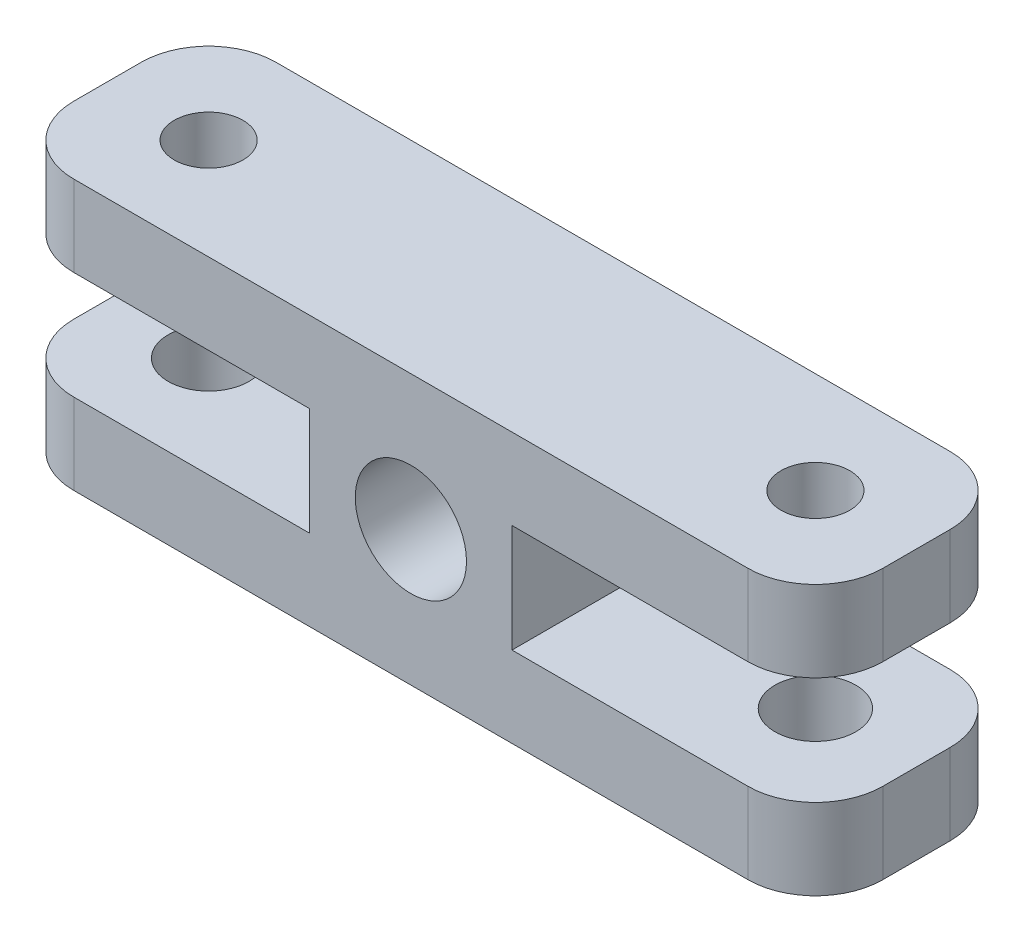
SolidWorks part; units mm, degrees
material "A3"
ref_plane "前视基准面" through (0, 0, 0) normal (0, 0, 1) x (1, 0, 0)
ref_plane "上视基准面" through (0, 0, 0) normal (0, 1, 0) x (1, 0, 0)
ref_plane "右视基准面" through (0, 0, 0) normal (1, 0, 0) x (0, 0, -1)
sketch "草图1" plane through (0, 0, 0) normal (0, 0, 1) x (1, 0, 0)
  line L0 (-89.7385, 0) -> (88.2601, 0) construction
  line L1 (0, 66.3798) -> (0, -71.7277) construction
  line L3 (-60, -20) -> (60, -20)
  line L4 (-60, -20) -> (-60, 20)
  line L5 (-60, 20) -> (60, 20)
  line L6 (60, -20) -> (60, 20)
  line L7 (-60, -20) -> (60, 20) construction
  line L8 (-60, 20) -> (60, -20) construction
  point P5 (0, 0)
  dimension "D1" = 120
  dimension "D2" = 40
extrude "凸台-拉伸1" add sketch "草图1" along normal mid plane 30
sketch "草图5" plane through (0, -20, 0) normal (0, -1, 0) x (-1, 0, 0)
  line L0 (0, 16.0404) -> (0, -23.8694) construction
  line L1 (-52.591, 0) -> (48.9492, 0) construction
  circle A0 centre (45, 0) radius 6
  circle A1 centre (-45, 0) radius 6
  dimension "D1" = 12
  dimension "D2" = 90
extrude "切除-拉伸2" cut sketch "草图5" against normal blind 20
hole_wizard "M18x1.5 螺纹孔1" positions "草图6" profile "草图7" tap size "M18x1.5" standard "GB" end condition through all
sketch "草图6" plane through (0, 0, 15) normal (0, 0, 1) x (1, 0, 0)
  point P0 (0, 0)
sketch "草图7" plane through (0, 0, 15) normal (1, 0, 0) x (0, -1, 0)
  line L0 (0, 0) -> (0, 30)
  line L1 (0, 30) -> (8.25, 30)
  line L2 (8.25, 30) -> (8.25, 0)
  line L5 (8.25, 0) -> (0, 0)
  line L11 (0, -6.35) -> (0, 107.95) construction
  dimension "通孔螺纹孔钻头直径" = 16.5
  dimension "通孔螺纹孔钻头深度" = 30
cosmetic thread "孔螺蚊线1" parameters "D2"=18
sketch "草图8" plane through (0, 0, 15) normal (0, 0, 1) x (1, 0, 0)
  line L0 (-60, 20) -> (-60, -20) construction
  line L1 (-60, 8) -> (-15, 8)
  line L2 (-60, 8) -> (-60, -8)
  line L3 (-60, -8) -> (-15, -8)
  line L4 (-15, 8) -> (-15, -8)
  line L5 (44.3488, 0) -> (-45.3176, 0) construction
  line L6 (0, 22.3359) -> (0, -22.1206) construction
  line L7 (15, 8) -> (15, -8)
  line L8 (60, -8) -> (15, -8)
  line L9 (60, 8) -> (60, -8)
  line L10 (60, 8) -> (15, 8)
  dimension "D1" = 30
  dimension "D2" = 16
extrude "切除-拉伸3" cut sketch "草图8" against normal through all
fillet "圆角1" radius 10 8 edges at (60, 14, 15) (60, -14, 15) (60, -14, -15) (60, 14, -15) (-60, 14, 15) (-60, -14, 15) (-60, 14, -15) (-60, -14, -15)
hole_wizard "M12 螺纹孔1" positions "草图9" profile "草图10" tap size "M12" standard "GB"
sketch "草图9" plane through (0, 20, 0) normal (0, 1, 0) x (1, 0, 0)
  line L0 (0, 18.3541) -> (0, -19.1932) construction
  line L3 (72.3314, 0) -> (-70.2183, 0) construction
  point P0 (-45, 0)
  point P10 (45, 0)
  dimension "D1" = 90
cosmetic thread "孔螺蚊线2" parameters "D1"=12, "D2"=12
cosmetic thread "孔螺蚊线3" parameters "D1"=12, "D2"=12
sketch "草图10" plane through (-45, 20, 0) normal (1, 0, 0) x (0, 0, 1)
  line L0 (0, 0) -> (0, 18.0644)
  line L1 (0, 18.0644) -> (5.1, 15)
  line L2 (5.1, 15) -> (5.1, 0)
  line L5 (5.1, 0) -> (0, 0)
  line L10 (0, 18.0644) -> (-5.1, 15) construction
  line L11 (0, -6.35) -> (0, 107.95) construction
  dimension "螺纹孔钻头直径" = 10.2
  dimension "螺纹孔钻头深度" = 15
  dimension "导头角度" = 118
